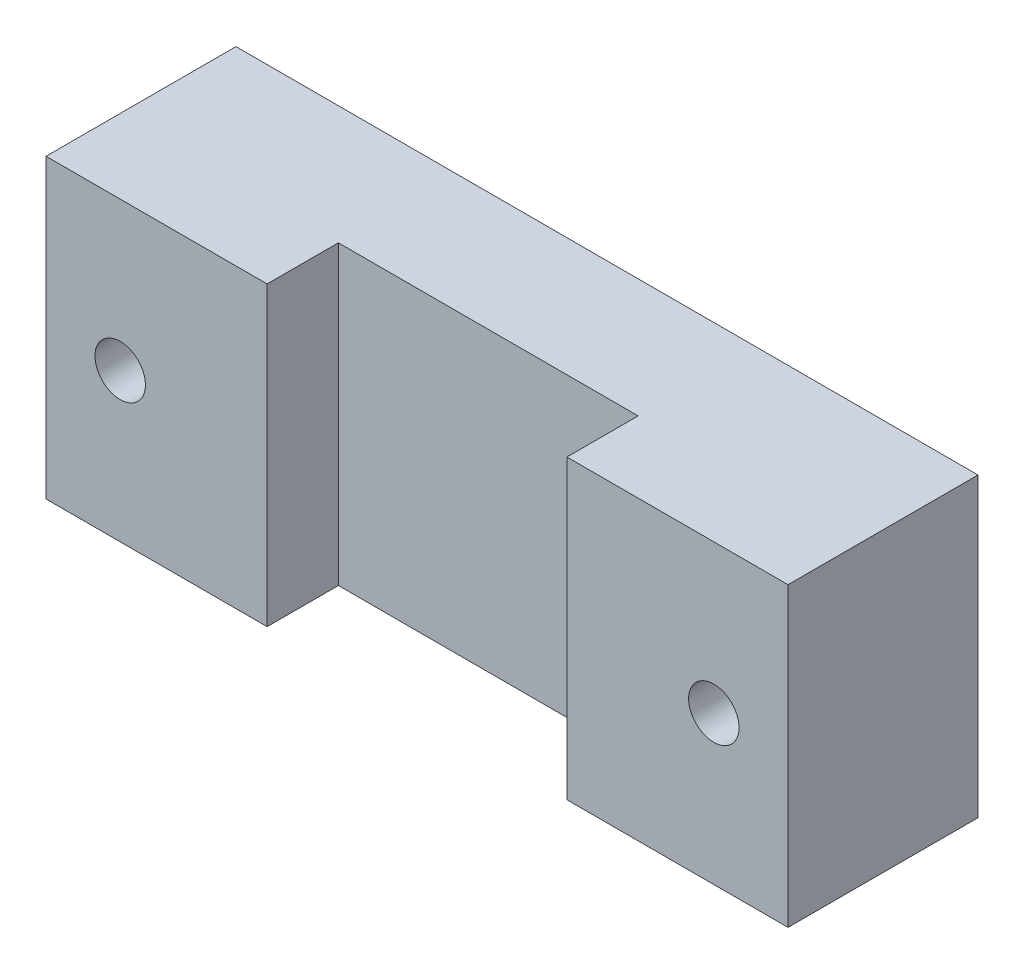
SolidWorks part; units mm, degrees
ref_plane "Спереди" through (0, 0, 0) normal (0, 0, 1) x (1, 0, 0)
ref_plane "Сверху" through (0, 0, 0) normal (0, 1, 0) x (1, 0, 0)
ref_plane "Справа" through (0, 0, 0) normal (1, 0, 0) x (0, 0, -1)
sketch "Sketch2" plane through (0, 0, 0) normal (0, 0, 1) x (1, 0, 0)
  line L0 (20, 0) -> (-20, 0) construction
  line L1 (25, -10) -> (-25, -10)
  line L2 (25, -10) -> (25, 10)
  line L3 (25, 10) -> (-25, 10)
  line L4 (-25, -10) -> (-25, 10)
  line L5 (25, -10) -> (-25, 10) construction
  line L6 (25, 10) -> (-25, -10) construction
  circle A0 centre (-20, 0) radius 1.7
  circle A1 centre (20, 0) radius 1.7
  point P0 (0, 0)
  point P9 (0, 0)
  dimension "D4" = 3.4
  dimension "D1" = 20
  dimension "D2" = 50
  dimension "D3" = 40
extrude "Boss-Extrude1" add sketch "Sketch2" along normal blind 8
sketch "Sketch5" plane through (0, -10, 0) normal (0, -1, 0) x (1, 0, 0)
  line L0 (-25, 8) -> (-25, 12.8)
  line L1 (-25, 8) -> (25, 8) construction
  line L2 (-25, 12.8) -> (-10.1, 12.8)
  line L3 (-10.1, 12.8) -> (-10.1, 8)
  line L4 (-10.1, 8) -> (10.1, 8)
  line L5 (10.1, 8) -> (10.1, 12.8)
  line L6 (10.1, 12.8) -> (25, 12.8)
  line L7 (25, 12.8) -> (25, 8)
  line L8 (25, 8) -> (-25, 8) construction
  line L9 (-25, 0) -> (25, 0) construction
  line L10 (0, 8) -> (0, 0) construction
  line L11 (-25, 8) -> (-25, 0) construction
  arc A0 (-25, 8) -> (25, 8) centre (0, 43.0625) ccw
  point P17 (0, 0)
  dimension "D1" = 20.2
  dimension "D3" = 4.8
extrude "Boss-Extrude2" add sketch "Sketch5" against normal up to surface (20 mm away) up to face at (0, 10, 4)
sketch "Sketch6" plane through (0, 0, 0) normal (0, 0, -1) x (-1, 0, 0)
  circle A0 centre (20, 0) radius 3.75
  circle A1 centre (-20, 0) radius 3.75
  dimension "D1" = 7.5
extrude "Cut-Extrude1" cut sketch "Sketch6" against normal blind 4
sketch "Sketch7" plane through (0, 0, 0) normal (0, 0, -1) x (-1, 0, 0)
  circle A0 centre (20, 0) radius 1.7
  circle A1 centre (20, 0) radius 1.7 construction
  circle A2 centre (-20, 0) radius 1.7
  circle A4 centre (-20, 0) radius 1.7 construction
extrude "Cut-Extrude2" cut sketch "Sketch7" against normal through all
